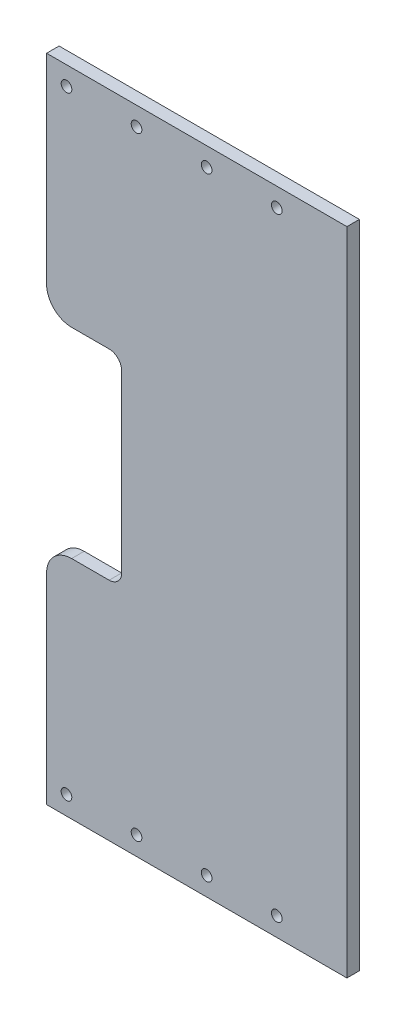
SolidWorks part; units mm, degrees
material "Hexcel AS4C (3000 Filaments)"
ref_plane "Front Plane" through (0, 0, 0) normal (0, 0, 1) x (1, 0, 0)
ref_plane "Top Plane" through (0, 0, 0) normal (0, 1, 0) x (1, 0, 0)
ref_plane "Right Plane" through (0, 0, 0) normal (1, 0, 0) x (0, 0, -1)
sketch "Sketch1" plane through (0, 0, 0) normal (0, 0, 1) x (1, 0, 0)
  line L1 (38.0982, 82.55) -> (38.0984, -82.55)
  line L2 (-38.0982, -82.55) -> (38.0984, -82.55)
  line L3 (-38.0982, -82.55) -> (-38.0982, -31.651)
  line L6 (-22.2233, -25.301) -> (-31.7482, -25.301)
  line L7 (-19.0483, 22.324) -> (-19.0483, -22.126)
  line L8 (-31.7482, 25.499) -> (-22.2233, 25.499)
  line L10 (-38.0982, -82.55) -> (38.0982, 82.55) construction
  line L11 (-38.0982, 82.55) -> (38.0984, -82.55) construction
  line L12 (-38.0982, 82.55) -> (-38.0982, 31.849)
  line L13 (-38.0982, 82.55) -> (38.0982, 82.55)
  circle A0 centre (2.5053, -77.7875) radius 1.3526
  circle A1 centre (-15.2747, -77.7875) radius 1.3526
  circle A2 centre (-33.0548, -77.7875) radius 1.3526
  circle A3 centre (2.5051, 77.7875) radius 1.3526
  circle A4 centre (-15.2749, 77.7875) radius 1.3526
  ellipse E0 centre (20.2983, -77.7875) end of major axis (20.2983, -79.14) minor radius 1.3525
  ellipse E1 centre (20.2981, 77.7875) end of major axis (20.2981, 76.435) minor radius 1.3525
  ellipse E2 centre (-33.0418, 77.7875) end of major axis (-33.0418, 76.435) minor radius 1.3525
  ellipse E3 centre (-31.7482, -31.651) end of major axis (-31.7482, -38.001) minor radius 6.35 (-31.7482, -25.301) -> (-38.0982, -31.651) ccw
  ellipse E4 centre (-22.2233, -22.126) end of major axis (-22.2233, -18.951) minor radius 3.175 (-22.2233, -25.301) -> (-19.0483, -22.126) ccw
  ellipse E5 centre (-22.2233, 22.324) end of major axis (-22.2233, 25.499) minor radius 3.175 (-19.0483, 22.324) -> (-22.2233, 25.499) ccw
  ellipse E6 centre (-31.7482, 31.849) end of major axis (-31.7482, 25.499) minor radius 6.35 (-38.0982, 31.849) -> (-31.7482, 25.499) ccw
extrude "Boss-Extrude2" add sketch "Sketch1" along normal blind 3.175
